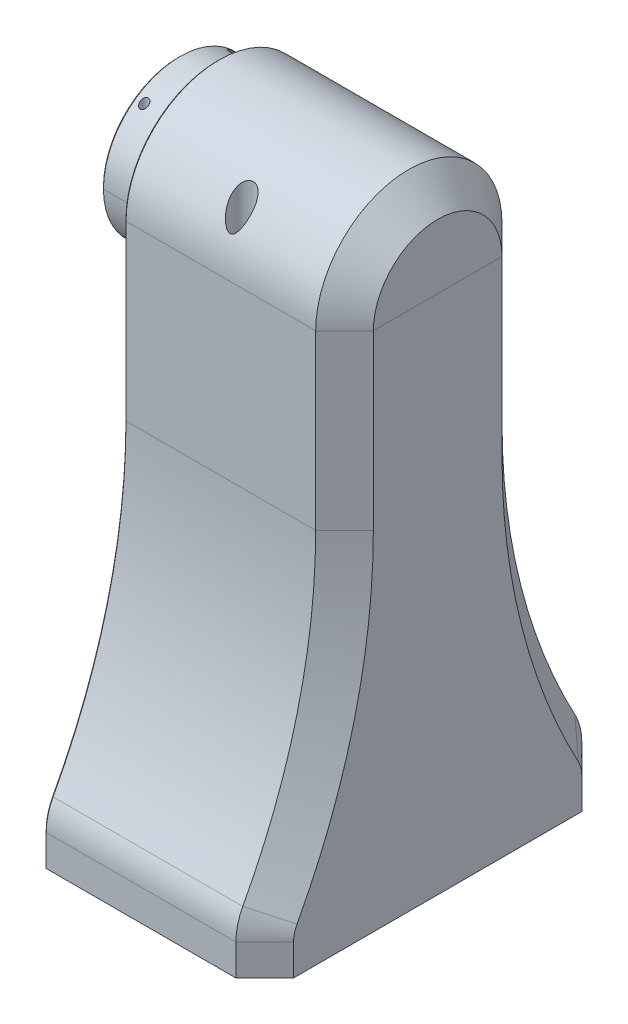
SolidWorks part; units mm, degrees
ref_plane "Front Plane" through (0, 0, 0) normal (0, 0, 1) x (1, 0, 0)
ref_plane "Top Plane" through (0, 0, 0) normal (0, 1, 0) x (1, 0, 0)
ref_plane "Right Plane" through (0, 0, 0) normal (1, 0, 0) x (0, 0, -1)
sketch "Sketch1" plane through (0, 0, 0) normal (0, 0, 1) x (1, 0, 0)
  line L1 (0, 0) -> (0, 5.0292)
  line L2 (0, 5.0292) -> (5.0546, 5.0292)
  line L3 (5.0546, 5.0292) -> (5.0546, 13.7668)
  line L4 (5.0546, 13.7668) -> (36.8046, 13.7668)
  line L5 (43.1546, 13.7668) -> (43.1546, 13.7414)
  line L6 (53.3146, 0) -> (0, 0)
  line L8 (43.1546, 13.7414) -> (53.3146, 13.7414)
  line L9 (53.3146, 13.7414) -> (53.3146, 0)
  line L10 (36.8046, 13.7668) -> (36.8046, 14.224)
  line L11 (36.8046, 14.224) -> (40.6146, 14.224)
  line L12 (40.6146, 14.224) -> (40.6146, 13.7668)
  line L13 (40.6146, 13.7668) -> (43.1546, 13.7668)
  point P8 (38.7096, 14.224)
  dimension "D1" = 5.0546
  dimension "D2" = 31.75
  dimension "D3" = 5.0292
  dimension "D4" = 38.1
  dimension "D5" = 13.7668
  dimension "D6" = 0.0254
  dimension "D7" = 10.16
  dimension "D8" = 35.56
  dimension "D9" = 14.224
revolve "Revolve1" add sketch "Sketch1" angle 360 about L6
sketch "Sketch2" plane through (5.0546, 0, 0) normal (-1, 0, 0) x (0, 0, 1)
  line L0 (0, -14.6304) -> (0, -12.9032) construction
  line L1 (-1.4224, -14.6304) -> (-1.4224, -12.9032)
  line L2 (1.4224, -14.6304) -> (1.4224, -12.9032)
  line L3 (0, 14.6304) -> (0, 12.9032) construction
  line L4 (1.4224, 14.6304) -> (1.4224, 12.9032)
  line L5 (-1.4224, 14.6304) -> (-1.4224, 12.9032)
  arc A0 (-1.4224, -14.6304) -> (1.4224, -14.6304) centre (0, -14.6304) ccw
  arc A1 (1.4224, -12.9032) -> (-1.4224, -12.9032) centre (0, -12.9032) ccw
  arc A2 (1.4224, 14.6304) -> (-1.4224, 14.6304) centre (0, 14.6304) ccw
  arc A3 (-1.4224, 12.9032) -> (1.4224, 12.9032) centre (0, 12.9032) ccw
  circle A4 centre (0, 0) radius 13.7668 construction
  point P3 (0, -13.7668)
  point P8 (0, 13.7668)
  dimension "D1" = 1.4224
  dimension "D2" = 2.286
extrude "Cut-Extrude1" cut sketch "Sketch2" against normal through all from offset 33.528 offset against normal yes
sketch "Sketch3" plane through (0, 0, 0) normal (1, 0, 0) x (0, 0, -1)
  line L0 (0, -114.681) -> (38.1, -114.681)
  line L2 (0, 20.5232) -> (0, -114.681)
  line L3 (20.5232, 0) -> (20.5232, -38.1)
  line L4 (38.1, -107.8008) -> (38.1, -114.681)
  arc A0 (20.5232, 0) -> (0, 20.5232) centre (0, 0) ccw
  arc A2 (20.5232, -38.1) -> (36.5813, -101.7785) centre (154.8108, -38.1) ccw
  arc A3 (36.5813, -101.7785) -> (38.1, -107.8008) centre (25.4, -107.8008) cw
  point P15 (38.1, -104.521)
  dimension "D3" = 41.0464
  dimension "D7" = 12.7
  dimension "D1" = 114.681
  dimension "D2" = 38.1
  dimension "D5" = 38.1
  dimension "D6" = 10.16
extrude "Boss-Extrude1" add sketch "Sketch3" along normal offset from surface (48.514 mm away) 3.81 from offset 8.6106 separate body up to face at (53.3146, 0, 0) offset beyond the face yes
sketch "Sketch4" plane through (8.6106, 0, 0) normal (-1, 0, 0) x (0, 0, 1)
  circle A0 centre (0, 0) radius 16.8783
  dimension "D1" = 33.7566
extrude "Boss-Extrude2" add sketch "Sketch4" along normal up to surface (8.6106 mm away) up to plane "Right Plane"
combine bodies "Combine1" operation type subtract main body 108 bodies to subtract 106
chamfer "Chamfer1" distance 6.35 angle 45 5 edges at (57.1246, -111.2409, -38.1) (57.1246, -104.6954, -37.7145) (57.1246, -70.936, -24.5996) (57.1246, -19.05, -20.5232) (57.1246, 14.5121, -14.5121)
sketch "Sketch9" plane through (0, 0, 0) normal (0, 1, 0) x (1, 0, 0)
  line L0 (2.286, 9.779) -> (2.286, -9.779) construction
  line L1 (0, 16.8783) -> (0, -16.8783) construction
  circle A0 centre (2.286, 9.779) radius 0.889
  circle A1 centre (2.286, -9.779) radius 0.889
  point P4 (2.286, 0)
  dimension "D2" = 1.778
  dimension "D1" = 19.558
  dimension "D3" = 2.286
extrude "Cut-Extrude5" cut sketch "Sketch9" against normal through all both and the other way through all
chamfer "Chamfer2" distance 0.381 angle 45 8 edges at (8.6106, -111.2409, -38.1) (8.6106, -104.6954, -37.7145) (8.6106, -70.936, -24.5996) (8.6106, -19.05, -20.5232) (8.6106, 14.5121, -14.5121) (0, 0, -16.8783) (0, 0, -5.0292) (5.0546, 0, -5.0292)
split "Split1" trim tools "Top Plane" bodies to split 117 resulting bodies 110 111
sketch "Sketch5" plane through (0, 0, 0) normal (0, 1, 0) x (1, 0, 0)
  line L0 (8.6106, 289.0984) -> (8.6106, 20.5232) construction
  line L1 (13.6906, 0) -> (36.0426, 0)
  line L2 (13.6906, 0) -> (13.6906, 8.6868)
  line L3 (16.2306, 11.2268) -> (33.5026, 11.2268)
  line L4 (36.0426, 0) -> (36.0426, 8.6868)
  line L5 (38.5826, 1.4224) -> (38.5826, 0) construction
  line L7 (5.0546, 13.7668) -> (36.8046, 13.7668) construction
  arc A0 (33.5026, 11.2268) -> (36.0426, 8.6868) centre (33.5026, 8.6868) cw
  arc A1 (13.6906, 8.6868) -> (16.2306, 11.2268) centre (16.2306, 8.6868) cw
  dimension "D3" = 2.54
  dimension "D1" = 5.08
  dimension "D2" = 2.54
  dimension "D4" = 2.54
extrude "Cut-Extrude2" cut sketch "Sketch5" against normal through all
sketch "Sketch7" plane through (0, 0, 0) normal (0, 1, 0) x (1, 0, 0)
  line L0 (13.6906, 0) -> (36.0426, 0) construction
  line L1 (33.5026, 11.2268) -> (49.5046, 11.2268)
  line L2 (33.5026, 11.2268) -> (33.5026, 0)
  line L3 (33.5026, 0) -> (52.0446, 0)
  line L4 (52.0446, 8.6868) -> (52.0446, 0)
  line L5 (57.1246, 14.1732) -> (57.1246, 0) construction
  arc A0 (49.5046, 11.2268) -> (52.0446, 8.6868) centre (49.5046, 8.6868) cw
  arc A1 (16.2306, 11.2268) -> (13.6906, 8.6868) centre (16.2306, 8.6868) ccw construction
  dimension "D1" = 5.08
extrude "Cut-Extrude4" cut sketch "Sketch7" against normal through all from offset 30.48 offset against normal yes
sketch "Sketch6" plane through (0, 0, 0) normal (0, 1, 0) x (1, 0, 0)
  line L0 (53.3146, 13.7414) -> (53.3146, 0) construction
  line L1 (33.5026, 11.2268) -> (50.7746, 11.2268)
  line L2 (33.5026, 11.2268) -> (33.5026, 4.8768)
  line L3 (33.5026, 4.8768) -> (50.7746, 4.8768)
  line L4 (53.3146, 8.6868) -> (53.3146, 7.4168)
  arc A0 (50.7746, 11.2268) -> (53.3146, 8.6868) centre (50.7746, 8.6868) cw
  arc A1 (50.7746, 4.8768) -> (53.3146, 7.4168) centre (50.7746, 7.4168) ccw
  point P9 (53.3146, 11.2268)
  point P12 (53.3146, 4.8768)
  dimension "D2" = 2.54
  dimension "D1" = 6.35
extrude "Cut-Extrude3" cut sketch "Sketch6" against normal blind 22.86
fillet "Fillet2" radius 3.81 1 edges at (36.0426, -17.867, -4.8768)
hole_wizard "M5x0.8 Tapped Hole1" positions "Sketch10" profile "Sketch12" tap size "M5x0.8" standard "ANSI Metric"
sketch "Sketch10" plane through (0, -114.681, 0) normal (0, -1, 0) x (-1, 0, 0)
  line L0 (-57.1246, 0) -> (-57.1246, 31.75) construction
  line L1 (-8.6106, 0) -> (-8.6106, 37.719) construction
  point P0 (-19.0246, 30.48)
  point P2 (-50.7746, 30.48)
  dimension "D1" = 31.75
  dimension "D2" = 6.35
  dimension "D3" = 30.48
  dimension "D4" = 10.414
  dimension "D5" = 42.164
sketch "Sketch12" plane through (19.0246, -114.681, -30.48) normal (1, 0, 0) x (0, 0, -1)
  line L0 (0, 0) -> (0, 16.2478)
  line L1 (0, 16.2478) -> (2.1, 14.986)
  line L2 (2.1, 14.986) -> (2.1, 0)
  line L5 (2.1, 0) -> (0, 0)
  line L10 (0, 16.2478) -> (-2.1, 14.986) construction
  line L11 (0, -6.35) -> (0, 107.95) construction
  dimension "Tap Drill Dia." = 4.2
  dimension "Tap Drill Depth" = 14.986
  dimension "Drill Angle" = 118
cosmetic thread "Hole Thread1" parameters "D1"=12.7, "D2"=5
cosmetic thread "Hole Thread2" parameters "D1"=12.7, "D2"=5
sketch "Sketch13" plane through (0, 0, 0) normal (0, 1, 0) x (1, 0, 0)
  circle A0 centre (30.48, 16.51) radius 2.54
  dimension "D1" = 5.08
  dimension "D2" = 16.51
  dimension "D3" = 30.48
extrude "Cut-Extrude6" cut sketch "Sketch13" along normal through all from offset 4.572
hole_wizard "M2 Clearance Hole1" positions "Sketch14" profile "Sketch15" hole size "M2" standard "ANSI Metric" end condition through all
sketch "Sketch14" plane through (0, 4.572, 0) normal (0, 1, 0) x (1, 0, 0)
  point P0 (30.48, 16.51)
sketch "Sketch15" plane through (30.48, 4.572, -16.51) normal (1, 0, 0) x (0, 0, 1)
  line L0 (0, 0) -> (0, 119.253)
  line L1 (0, 119.253) -> (1.1, 119.253)
  line L2 (1.1, 119.253) -> (1.1, 0)
  line L5 (1.1, 0) -> (0, 0)
  line L11 (0, -6.35) -> (0, 107.95) construction
  dimension "Thru Hole Dia." = 2.2
  dimension "Thru Hole Depth" = 119.253
hole_wizard "M2x0.4 Tapped Hole1" positions "Sketch16" profile "Sketch17" tap size "M2x0.4" standard "ANSI Metric"
sketch "Sketch16" plane through (0, 0, 0) normal (0, 1, 0) x (1, 0, 0)
  point P0 (30.48, 16.51)
sketch "Sketch17" plane through (30.48, 0, -16.51) normal (1, 0, 0) x (0, 0, 1)
  line L0 (0, 0) -> (0, 14.4507)
  line L1 (0, 14.4507) -> (0.8, 13.97)
  line L2 (0.8, 13.97) -> (0.8, 0)
  line L5 (0.8, 0) -> (0, 0)
  line L10 (0, 14.4507) -> (-0.8, 13.97) construction
  line L11 (0, -6.35) -> (0, 107.95) construction
  dimension "Tap Drill Dia." = 1.6
  dimension "Tap Drill Depth" = 13.97
  dimension "Drill Angle" = 118
cosmetic thread "Hole Thread3" parameters "D1"=12.7, "D2"=2
mirror "Mirror1" about plane through (0, 0, 0) normal (0, 0, 1) of bodies 121 120 111 110
cosmetic thread "Hole Thread4" parameters "D1"=12.7, "D2"=2
cosmetic thread "Hole Thread5" parameters "D1"=12.7, "D2"=5
cosmetic thread "Hole Thread6" parameters "D1"=12.7, "D2"=5
delete or keep bodies "Body-Delete/Keep 1" [suppressed] type keep bodies bodies 112
